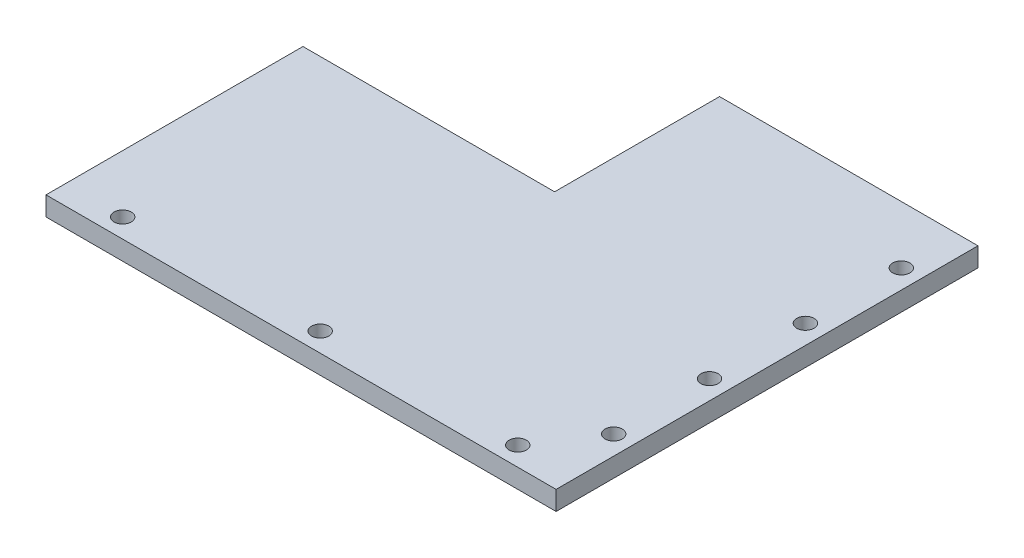
SolidWorks part; units mm, degrees
ref_plane "Front Plane" through (0, 0, 0) normal (0, 0, 1) x (1, 0, 0)
ref_plane "Top Plane" through (0, 0, 0) normal (0, 1, 0) x (1, 0, 0)
ref_plane "Right Plane" through (0, 0, 0) normal (1, 0, 0) x (0, 0, -1)
sketch "Sketch1" plane through (0, 0, 0) normal (0, 1, 0) x (1, 0, 0)
  line L0 (0, 55.7333) -> (0, 12.7333)
  line L1 (0, 55.7333) -> (67.3866, 55.7333)
  line L2 (-65.6134, 12.7333) -> (-65.6134, -54.2667)
  line L3 (-65.6134, -54.2667) -> (67.3866, -54.2667)
  line L4 (67.3866, 55.7333) -> (67.3866, -54.2667)
  line L5 (-15.8117, 12.7333) -> (67.3866, -54.2667) construction
  line L6 (-65.6134, -54.2667) -> (67.3866, 55.7333) construction
  line L7 (0, 12.7333) -> (-65.6134, 12.7333)
  line L8 (57.3866, 55.7333) -> (57.3866, -54.2667) construction
  line L9 (62.3866, 55.7333) -> (62.3866, -54.2667) construction
  line L10 (57.3866, 0.7333) -> (67.3866, 0.7333) construction
  line L11 (-65.6134, -44.2667) -> (67.3866, -44.2667) construction
  line L12 (-65.6134, -49.2667) -> (67.3866, -49.2667) construction
  line L13 (0.8866, -54.2667) -> (0.8866, -44.2667) construction
  circle A0 centre (62.3866, 40.7333) radius 2.25
  circle A1 centre (62.3866, 15.7333) radius 2.25
  circle A2 centre (62.3866, -9.2667) radius 2.25
  circle A3 centre (62.3866, -34.2667) radius 2.25
  circle A4 centre (0.8866, -49.2667) radius 2.25
  circle A5 centre (-50.6134, -49.2667) radius 2.25
  circle A6 centre (52.3866, -49.2667) radius 2.25
  point P0 (0, 0)
  point P6 (-65.6134, 12.7333)
  point P7 (0, 55)
  point P14 (57.3866, 55.7333)
  point P18 (62.3866, 40.7333)
  dimension "D7" = 4
  dimension "D10" = 4.5
  dimension "D11" = 15
  dimension "D1" = 67
  dimension "D2" = 110
  dimension "D3" = 133
  dimension "D4" = 10
  dimension "D5" = 5
  dimension "D6" = 15
  dimension "D8" = 10
  dimension "D9" = 5
extrude "Boss-Extrude1" add sketch "Sketch1" along normal blind 5
